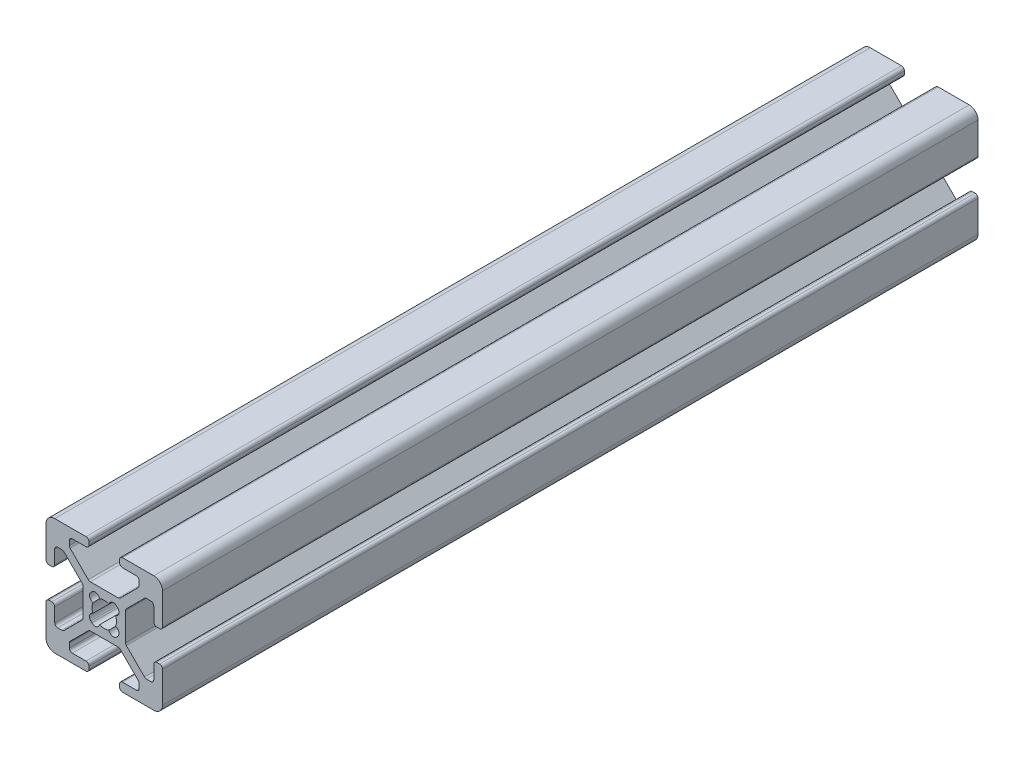
SolidWorks part; units mm, degrees
material "6061 Alloy"
ref_plane "Front Plane" through (0, 0, 0) normal (0, 0, 1) x (1, 0, 0)
ref_plane "Top Plane" through (0, 0, 0) normal (0, 1, 0) x (1, 0, 0)
ref_plane "Right Plane" through (0, 0, 0) normal (1, 0, 0) x (0, 0, -1)
ref_plane "Plane1" through (0, 0, 4000) normal (0, 0, 1) x (1, 0, 0)
sketch "Sketch1" plane through (0, 0, 4000) normal (0, 0, 1) x (1, 0, 0)
  line B0 (10, 3.138) -> (10, 8.5)
  line B1 (8.5, 10) -> (3.138, 10)
  line B2 (2.63, 9.492) -> (2.63, 9.008)
  line B3 (3.138, 8.5) -> (5.487, 8.5)
  line B4 (5.995, 7.992) -> (5.995, 7.2661)
  line B5 (5.8462, 6.9069) -> (2.7431, 3.8038)
  line B6 (2.3839, 3.655) -> (-2.3839, 3.655)
  line B7 (-2.7431, 3.8038) -> (-5.8462, 6.9069)
  line B8 (-5.995, 7.2661) -> (-5.995, 7.992)
  line B9 (-5.487, 8.5) -> (-3.138, 8.5)
  line B10 (-2.63, 9.008) -> (-2.63, 9.492)
  line B11 (-3.138, 10) -> (-8.5, 10)
  line B12 (-10, 8.5) -> (-10, 3.138)
  line B13 (-9.492, 2.63) -> (-9.008, 2.63)
  line B14 (-8.5, 3.138) -> (-8.5, 5.487)
  line B15 (-7.992, 5.995) -> (-7.2661, 5.995)
  line B16 (-6.9069, 5.8462) -> (-3.8038, 2.7431)
  line B17 (-3.655, 2.3839) -> (-3.655, -2.3839)
  line B18 (-3.8038, -2.7431) -> (-6.9069, -5.8462)
  line B19 (-7.2661, -5.995) -> (-7.992, -5.995)
  line B20 (-8.5, -5.487) -> (-8.5, -3.138)
  line B21 (-9.008, -2.63) -> (-9.492, -2.63)
  line B22 (-10, -3.138) -> (-10, -8.5)
  line B23 (-8.5, -10) -> (-3.138, -10)
  line B24 (-2.63, -9.492) -> (-2.63, -9.008)
  line B25 (-3.138, -8.5) -> (-5.487, -8.5)
  line B26 (-5.995, -7.992) -> (-5.995, -7.2661)
  line B27 (-5.8462, -6.9069) -> (-2.7431, -3.8038)
  line B28 (-2.3839, -3.655) -> (2.3839, -3.655)
  line B29 (2.7431, -3.8038) -> (5.8462, -6.9069)
  line B30 (5.995, -7.2661) -> (5.995, -7.992)
  line B31 (5.487, -8.5) -> (3.138, -8.5)
  line B32 (2.63, -9.008) -> (2.63, -9.492)
  line B33 (3.138, -10) -> (8.5, -10)
  line B34 (10, -8.5) -> (10, -3.138)
  line B35 (9.492, -2.63) -> (9.008, -2.63)
  line B36 (8.5, -3.138) -> (8.5, -5.487)
  line B37 (7.992, -5.995) -> (7.2661, -5.995)
  line B38 (6.9069, -5.8462) -> (3.8038, -2.7431)
  line B39 (3.655, -2.3839) -> (3.655, 2.3839)
  line B40 (3.8038, 2.7431) -> (6.9069, 5.8462)
  line B41 (7.2661, 5.995) -> (7.992, 5.995)
  line B42 (8.5, 5.487) -> (8.5, 3.138)
  line B43 (9.008, 2.63) -> (9.492, 2.63)
  line B44 (-2.1249, -2.3045) -> (-2.3045, -2.1249)
  line B45 (-2.3045, 2.1249) -> (-2.1249, 2.3045)
  line B46 (2.1249, 2.3045) -> (2.3045, 2.1249)
  line B47 (2.3045, -2.1249) -> (2.1249, -2.3045)
  arc B48 (9.492, 2.63) -> (10, 3.138) centre (9.492, 3.138) ccw
  arc B49 (10, 8.5) -> (8.5, 10) centre (8.5, 8.5) ccw
  arc B50 (3.138, 10) -> (2.63, 9.492) centre (3.138, 9.492) ccw
  arc B51 (2.63, 9.008) -> (3.138, 8.5) centre (3.138, 9.008) ccw
  arc B52 (5.487, 8.5) -> (5.995, 7.992) centre (5.487, 7.992) cw
  arc B53 (5.995, 7.2661) -> (5.8462, 6.9069) centre (5.487, 7.2661) cw
  arc B54 (2.7431, 3.8038) -> (2.3839, 3.655) centre (2.3839, 4.163) cw
  arc B55 (-2.3839, 3.655) -> (-2.7431, 3.8038) centre (-2.3839, 4.163) cw
  arc B56 (-5.8462, 6.9069) -> (-5.995, 7.2661) centre (-5.487, 7.2661) cw
  arc B57 (-5.995, 7.992) -> (-5.487, 8.5) centre (-5.487, 7.992) cw
  arc B58 (-3.138, 8.5) -> (-2.63, 9.008) centre (-3.138, 9.008) ccw
  arc B59 (-2.63, 9.492) -> (-3.138, 10) centre (-3.138, 9.492) ccw
  arc B60 (-8.5, 10) -> (-10, 8.5) centre (-8.5, 8.5) ccw
  arc B61 (-10, 3.138) -> (-9.492, 2.63) centre (-9.492, 3.138) ccw
  arc B62 (-9.008, 2.63) -> (-8.5, 3.138) centre (-9.008, 3.138) ccw
  arc B63 (-8.5, 5.487) -> (-7.992, 5.995) centre (-7.992, 5.487) cw
  arc B64 (-7.2661, 5.995) -> (-6.9069, 5.8462) centre (-7.2661, 5.487) cw
  arc B65 (-3.8038, 2.7431) -> (-3.655, 2.3839) centre (-4.163, 2.3839) cw
  arc B66 (-3.655, -2.3839) -> (-3.8038, -2.7431) centre (-4.163, -2.3839) cw
  arc B67 (-6.9069, -5.8462) -> (-7.2661, -5.995) centre (-7.2661, -5.487) cw
  arc B68 (-7.992, -5.995) -> (-8.5, -5.487) centre (-7.992, -5.487) cw
  arc B69 (-8.5, -3.138) -> (-9.008, -2.63) centre (-9.008, -3.138) ccw
  arc B70 (-9.492, -2.63) -> (-10, -3.138) centre (-9.492, -3.138) ccw
  arc B71 (-10, -8.5) -> (-8.5, -10) centre (-8.5, -8.5) ccw
  arc B72 (-3.138, -10) -> (-2.63, -9.492) centre (-3.138, -9.492) ccw
  arc B73 (-2.63, -9.008) -> (-3.138, -8.5) centre (-3.138, -9.008) ccw
  arc B74 (-5.487, -8.5) -> (-5.995, -7.992) centre (-5.487, -7.992) cw
  arc B75 (-5.995, -7.2661) -> (-5.8462, -6.9069) centre (-5.487, -7.2661) cw
  arc B76 (-2.7431, -3.8038) -> (-2.3839, -3.655) centre (-2.3839, -4.163) cw
  arc B77 (2.3839, -3.655) -> (2.7431, -3.8038) centre (2.3839, -4.163) cw
  arc B78 (5.8462, -6.9069) -> (5.995, -7.2661) centre (5.487, -7.2661) cw
  arc B79 (5.995, -7.992) -> (5.487, -8.5) centre (5.487, -7.992) cw
  arc B80 (3.138, -8.5) -> (2.63, -9.008) centre (3.138, -9.008) ccw
  arc B81 (2.63, -9.492) -> (3.138, -10) centre (3.138, -9.492) ccw
  arc B82 (8.5, -10) -> (10, -8.5) centre (8.5, -8.5) ccw
  arc B83 (10, -3.138) -> (9.492, -2.63) centre (9.492, -3.138) ccw
  arc B84 (9.008, -2.63) -> (8.5, -3.138) centre (9.008, -3.138) ccw
  arc B85 (8.5, -5.487) -> (7.992, -5.995) centre (7.992, -5.487) cw
  arc B86 (7.2661, -5.995) -> (6.9069, -5.8462) centre (7.2661, -5.487) cw
  arc B87 (3.8038, -2.7431) -> (3.655, -2.3839) centre (4.163, -2.3839) cw
  arc B88 (3.655, 2.3839) -> (3.8038, 2.7431) centre (4.163, 2.3839) cw
  arc B89 (6.9069, 5.8462) -> (7.2661, 5.995) centre (7.2661, 5.487) cw
  arc B90 (7.992, 5.995) -> (8.5, 5.487) centre (7.992, 5.487) cw
  arc B91 (8.5, 3.138) -> (9.008, 2.63) centre (9.008, 3.138) ccw
  arc B92 (0.804, -1.9351) -> (-0.804, -1.9351) centre (0, 0) cw
  arc B93 (-0.804, -1.9351) -> (-2.1249, -2.3045) centre (-1.5684, -1.748) cw
  arc B94 (-2.3045, -2.1249) -> (-1.9351, -0.804) centre (-1.748, -1.5684) cw
  arc B95 (-1.9351, -0.804) -> (-1.9351, 0.804) centre (0, 0) cw
  arc B96 (-1.9351, 0.804) -> (-2.3045, 2.1249) centre (-1.748, 1.5684) cw
  arc B97 (-2.1249, 2.3045) -> (-0.804, 1.9351) centre (-1.5684, 1.748) cw
  arc B98 (-0.804, 1.9351) -> (0.804, 1.9351) centre (0, 0) cw
  arc B99 (0.804, 1.9351) -> (2.1249, 2.3045) centre (1.5684, 1.748) cw
  arc B100 (2.3045, 2.1249) -> (1.9351, 0.804) centre (1.748, 1.5684) cw
  arc B101 (1.9351, 0.804) -> (1.9351, -0.804) centre (0, 0) cw
  arc B102 (1.9351, -0.804) -> (2.3045, -2.1249) centre (1.748, -1.5684) cw
  arc B103 (2.1249, -2.3045) -> (0.804, -1.9351) centre (1.5684, -1.748) cw
sketch_block_instance "Block1-1"
sketch_block "Block1"
extrude "Boss-Extrude1" add sketch "Sketch1" against normal blind 140
